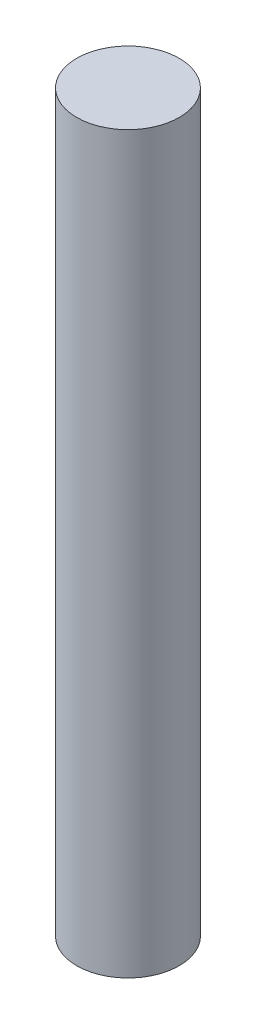
SolidWorks part; units mm, degrees
ref_plane "Front Plane" through (0, 0, 0) normal (0, 0, 1) x (1, 0, 0)
ref_plane "Top Plane" through (0, 0, 0) normal (0, 1, 0) x (1, 0, 0)
ref_plane "Right Plane" through (0, 0, 0) normal (1, 0, 0) x (0, 0, -1)
sketch "Sketch1" plane through (0, 0, 0) normal (0, 1, 0) x (1, 0, 0)
  circle A0 centre (0, 0) radius 3
  dimension "D1" = 6
extrude "Boss-Extrude1" add sketch "Sketch1" along normal blind 43
